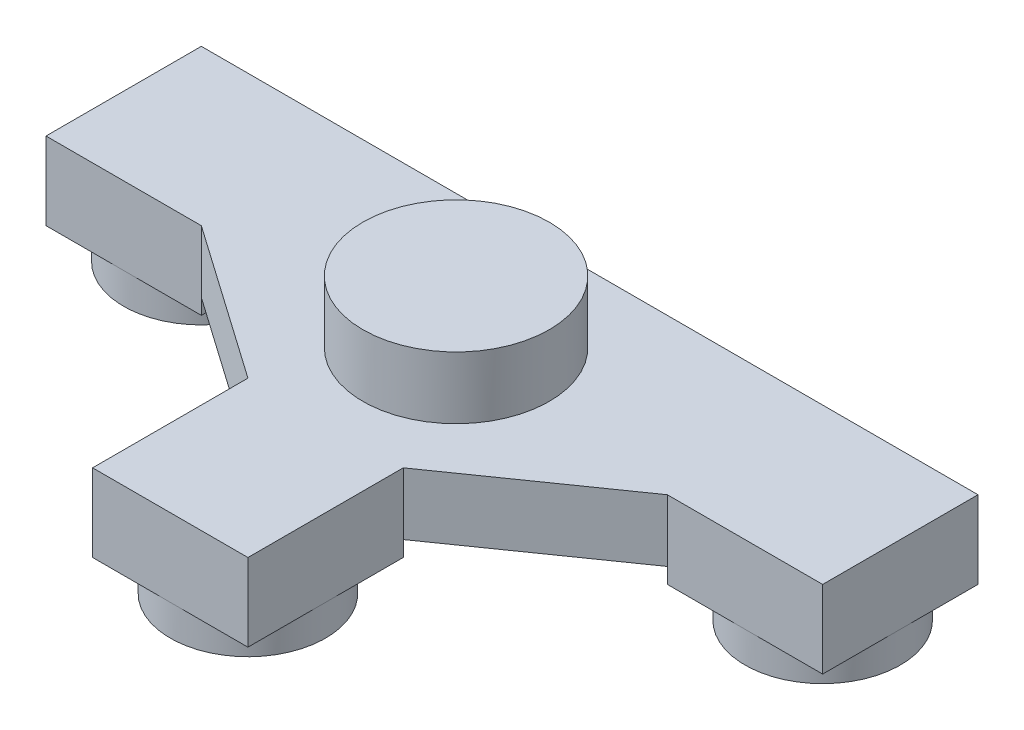
SolidWorks part; units mm, degrees
ref_plane "Front" through (0, 0, 0) normal (0, 0, 1) x (1, 0, 0)
ref_plane "Top" through (0, 0, 0) normal (0, 1, 0) x (1, 0, 0)
ref_plane "Right" through (0, 0, 0) normal (1, 0, 0) x (0, 0, -1)
sketch "草图1" plane through (0, 0, 0) normal (0, 1, 0) x (1, 0, 0)
  line L0 (-31.9558, 0) -> (0, 0) construction
  line L1 (-25, 5) -> (-15, 5)
  line L2 (-25, 5) -> (-25, -5)
  line L3 (-25, -5) -> (-15, -5)
  line L4 (-15, 5) -> (-15, -5)
  line L5 (15, 5) -> (25, 5)
  line L6 (15, 5) -> (15, -5)
  line L7 (15, -5) -> (25, -5)
  line L8 (25, 5) -> (25, -5)
  line L9 (-5, -12) -> (5, -12)
  line L10 (-5, -12) -> (-5, -22)
  line L11 (-5, -22) -> (5, -22)
  line L12 (5, -12) -> (5, -22)
  line L13 (0, 0) -> (0, 15.9462) construction
  dimension "D1" = 10
  dimension "D2" = 10
  dimension "D3" = 10
  dimension "D4" = 10
  dimension "D5" = 5
  dimension "D6" = 5
  dimension "D7" = 10
  dimension "D8" = 10
  dimension "D9" = 5
  dimension "D10" = 15
  dimension "D11" = 15
  dimension "D12" = 12
sketch "草图2" plane through (0, 0, 0) normal (0, 1, 0) x (1, 0, 0)
  line L0 (-25, -5) -> (-25, 23.5912) construction
  line L1 (25, -5) -> (25, 17.5149) construction
  line L2 (-25, 5) -> (25, 5) construction
  line L12 (-5, -22) -> (5, -22)
  line L19 (25, -5) -> (25, 5)
  line L20 (25, 5) -> (-25, 5)
  line L21 (-25, 5) -> (-25, -5)
  line L22 (-25, -5) -> (-15, -5)
  line L23 (-15, -5) -> (-5, -12)
  line L24 (-5, -12) -> (-5, -22)
  line L25 (5, -22) -> (5, -12)
  line L26 (5, -12) -> (15, -5)
  line L27 (15, -5) -> (25, -5)
extrude "凸台-拉伸1" add sketch "草图2" along normal blind 4
extrude "凸台-拉伸2" add sketch "草图1" against normal blind 1
sketch "草图5" plane through (0, 4, 0) normal (0, 1, 0) x (1, 0, 0)
  line L0 (0, 5) -> (0, -22) construction
  line L1 (25, 5) -> (-25, 5) construction
  line L2 (-5, -22) -> (5, -22) construction
  circle A0 centre (0, -3.6) radius 6
extrude "凸台-拉伸3" add sketch "草图5" along normal blind 4
sketch "草图6" plane through (0, -1, 0) normal (0, -1, 0) x (1, 0, 0)
  circle A0 centre (0, 17) radius 5
  circle A1 centre (20, 0) radius 5
  circle A2 centre (-20, 0) radius 5
extrude "凸台-拉伸4" add sketch "草图6" along normal blind 2
